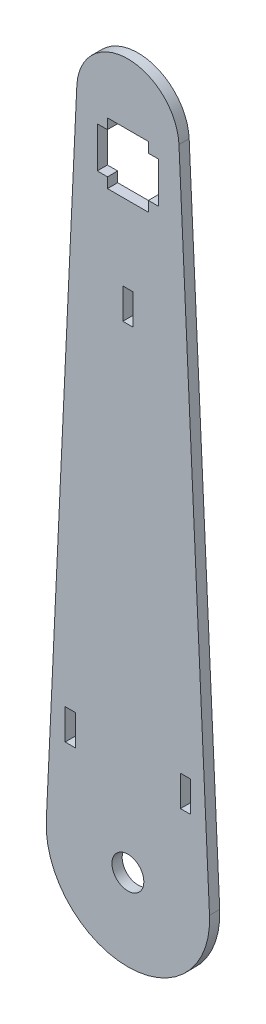
SolidWorks part; units mm, degrees
ref_plane "Front Plane" through (0, 0, 0) normal (0, 0, 1) x (1, 0, 0)
ref_plane "Top Plane" through (0, 0, 0) normal (0, 1, 0) x (1, 0, 0)
ref_plane "Right Plane" through (0, 0, 0) normal (1, 0, 0) x (0, 0, -1)
sketch "Sketch1" plane through (0, 0, 0) normal (0, 0, 1) x (1, 0, 0)
  line L0 (-25.3722, 1.1884) -> (-15.875, 203.9436)
  line L1 (25.3722, 1.1884) -> (15.875, 203.9436)
  line L2 (-6.35, 200.025) -> (6.35, 200.025)
  line L19 (-19.5072, 34.925) -> (-16.3322, 34.925)
  line L20 (-19.5072, 34.925) -> (-19.5072, 25.4)
  line L21 (-19.5072, 25.4) -> (-16.3322, 25.4)
  line L22 (-16.3322, 34.925) -> (-16.3322, 25.4)
  line L23 (-1.5875, 147.6375) -> (1.5875, 147.6375)
  line L24 (-1.5875, 147.6375) -> (-1.5875, 157.1625)
  line L25 (-1.5875, 157.1625) -> (1.5875, 157.1625)
  line L26 (1.5875, 147.6375) -> (1.5875, 157.1625)
  line L27 (-1.5875, 147.6375) -> (1.5875, 157.1625) construction
  line L28 (-1.5875, 157.1625) -> (1.5875, 147.6375) construction
  line L29 (16.3322, 25.4) -> (19.5072, 25.4)
  line L30 (16.3322, 25.4) -> (16.3322, 34.925)
  line L31 (16.3322, 34.925) -> (19.5072, 34.925)
  line L32 (19.5072, 25.4) -> (19.5072, 34.925)
  line L37 (6.35, 200.025) -> (6.35, 196.85)
  line L38 (6.35, 196.85) -> (9.525, 196.85)
  line L39 (9.525, 196.85) -> (9.525, 184.15)
  line L40 (9.525, 184.15) -> (6.35, 184.15)
  line L41 (6.35, 184.15) -> (6.35, 180.975)
  line L42 (6.35, 180.975) -> (-6.35, 180.975)
  line L43 (-6.35, 180.975) -> (-6.35, 184.15)
  line L44 (-6.35, 184.15) -> (-9.525, 184.15)
  line L45 (-9.525, 184.15) -> (-9.525, 196.85)
  line L46 (-9.525, 196.85) -> (-6.35, 196.85)
  line L47 (-6.35, 196.85) -> (-6.35, 200.025)
  line L48 (-9.525, 190.5) -> (9.525, 190.5) construction
  circle A0 centre (0, 0) radius 4.953
  arc A1 (25.3722, 1.1884) -> (-25.3722, 1.1884) centre (0, 0) cw
  arc A2 (-15.875, 203.9436) -> (15.875, 203.9436) centre (0, 203.2) cw
  point P12 (0, 152.4)
  point P34 (0, 190.5)
  dimension "D1" = 9.906
  dimension "D2" = 25.4
  dimension "D5" = 19.05
  dimension "D3" = 31.75
  dimension "D4" = 203.2
  dimension "D6" = 3.175
  dimension "D7" = 16.3322
  dimension "D8" = 9.525
  dimension "D9" = 25.4
  dimension "D10" = 50.8
  dimension "D11" = 16.3322
  dimension "D12" = 12.7
  dimension "D13" = 3.175
extrude "Boss-Extrude1" add sketch "Sketch1" along normal blind 3.175
